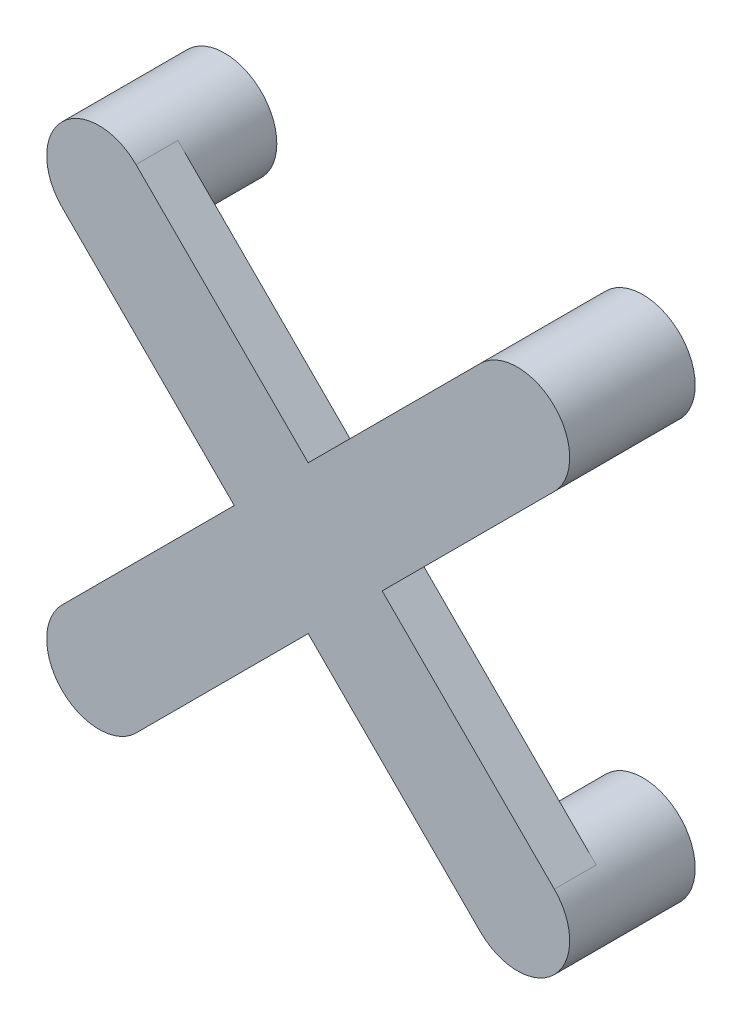
SolidWorks part; units mm, degrees
ref_plane "Plan de face" through (0, 0, 0) normal (0, 0, 1) x (1, 0, 0)
ref_plane "Plan de dessus" through (0, 0, 0) normal (0, 1, 0) x (1, 0, 0)
ref_plane "Plan de droite" through (0, 0, 0) normal (1, 0, 0) x (0, 0, -1)
sketch "Esquisse1" plane through (0, 0, 0) normal (0, 0, 1) x (1, 0, 0)
  circle A0 centre (-5, 5) radius 1.25
  circle A1 centre (5, 5) radius 1.25
  circle A2 centre (5, -5) radius 1.25
  circle A3 centre (-5, -5) radius 1.25
  point P8 (0, 0)
  point P9 (0, 0)
  point P10 (0, 0)
  point P11 (0, 0)
  point P12 (0, 0)
  point P13 (-8.6756, -6.1885)
  dimension "D1" = 2.5
  dimension "D2" = 10
  dimension "D3" = 10
  dimension "D4" = 5
  dimension "D5" = 5
extrude "Boss.-Extru.1" add sketch "Esquisse1" along normal blind 2
sketch "Esquisse2" plane through (0, 0, 2) normal (0, 0, 1) x (1, 0, 0)
  line L0 (-5.8839, -4.1161) -> (-1.7678, 0)
  line L1 (-1.7678, 0) -> (-5.8839, 4.1161)
  line L2 (-4.1161, 5.8839) -> (0, 1.7678)
  line L3 (0, 1.7678) -> (4.1161, 5.8839)
  line L4 (5.8839, 4.1161) -> (1.7678, 0)
  line L5 (1.7678, 0) -> (5.8839, -4.1161)
  line L6 (4.1161, -5.8839) -> (0, -1.7678)
  line L7 (0, -1.7678) -> (-4.1161, -5.8839)
  arc A0 (-4.1161, 5.8839) -> (-5.8839, 4.1161) centre (-5, 5) ccw
  circle A1 centre (-5, 5) radius 1.25 construction
  arc A2 (5.8839, 4.1161) -> (4.1161, 5.8839) centre (5, 5) ccw
  circle A3 centre (5, 5) radius 1.25 construction
  arc A4 (5.8839, -4.1161) -> (4.1161, -5.8839) centre (5, -5) cw
  arc A6 (-5.8839, -4.1161) -> (-4.1161, -5.8839) centre (-5, -5) ccw
  circle A7 centre (-5, -5) radius 1.25 construction
  circle A8 centre (5, -5) radius 1.25 construction
  point P16 (0.4408, -2.1012)
  point P26 (0, 3.0299)
  point P27 (0, 0)
  point P28 (0, 0)
  point P29 (0, 0)
  point P30 (-3.5146, 0)
  point P31 (3.2811, 0)
  point P34 (0, 4.1925)
  point P35 (0, -2.3768)
  dimension "D1" = 90
  dimension "D2" = 90
  dimension "D3" = 90
  dimension "D4" = 90
extrude "Boss.-Extru.2" add sketch "Esquisse2" along normal blind 1
